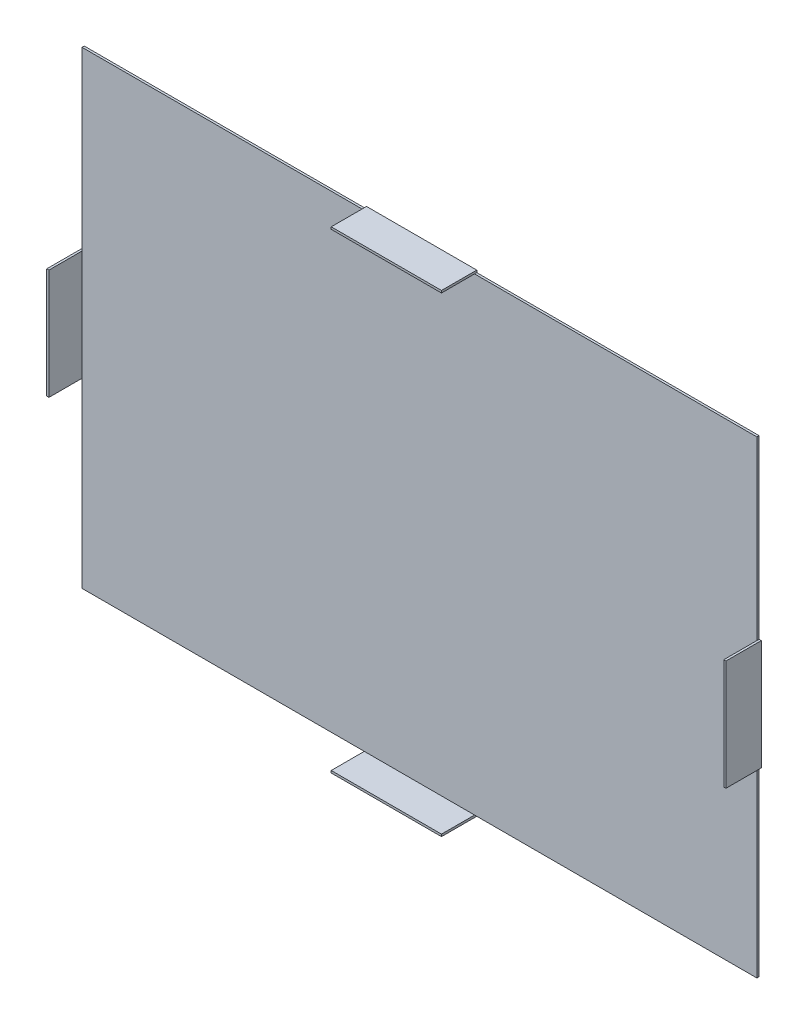
SolidWorks part; units mm, degrees
ref_plane "前基準面" through (0, 0, 0) normal (0, 0, 1) x (1, 0, 0)
ref_plane "上基準面" through (0, 0, 0) normal (0, 1, 0) x (1, 0, 0)
ref_plane "右基準面" through (0, 0, 0) normal (1, 0, 0) x (0, 0, -1)
sketch "草圖1" plane through (0, 0, 0) normal (0, 0, 1) x (1, 0, 0)
  line L1 (-301.7882, 224.6299) -> (310.2118, 224.6299)
  line L2 (-301.7882, 224.6299) -> (-301.7882, -200.3701)
  line L3 (-301.7882, -200.3701) -> (310.2118, -200.3701)
  line L4 (310.2118, 224.6299) -> (310.2118, -200.3701)
  dimension "D1" = 612
  dimension "D2" = 425
extrude "填料-伸長1" add sketch "草圖1" along normal blind 2
sketch "草圖2" plane through (0, -200.3701, 0) normal (0, -1, 0) x (1, 0, 0)
  line L0 (-301.7882, 0) -> (310.2118, 0) construction
  line L1 (-45.7882, 0) -> (54.2118, 0)
  line L2 (-45.7882, 0) -> (-45.7882, 32)
  line L3 (-45.7882, 32) -> (54.2118, 32)
  line L4 (54.2118, 0) -> (54.2118, 32)
  line L5 (-301.7882, 2) -> (-301.7882, 0) construction
  dimension "D1" = 32
  dimension "D2" = 100
  dimension "D3" = 256
extrude "填料-伸長2" add sketch "草圖2" along normal blind 2
sketch "草圖3" plane through (-301.7882, 0, 0) normal (-1, 0, 0) x (0, 0, 1)
  line L0 (0, 224.6299) -> (0, -200.3701) construction
  line L1 (0, 64.6299) -> (32, 64.6299)
  line L2 (0, 64.6299) -> (0, -35.3701)
  line L3 (0, -35.3701) -> (32, -35.3701)
  line L4 (32, 64.6299) -> (32, -35.3701)
  line L6 (2, 224.6299) -> (0, 224.6299) construction
  dimension "D1" = 32
  dimension "D2" = 100
  dimension "D3" = 160
extrude "填料-伸長3" add sketch "草圖3" along normal blind 2
sketch "草圖4" plane through (0, 224.6299, 0) normal (0, 1, 0) x (1, 0, 0)
  line L0 (310.2118, 0) -> (-301.7882, 0) construction
  line L1 (-45.7882, 0) -> (54.2118, 0)
  line L2 (-45.7882, 0) -> (-45.7882, -32)
  line L3 (-45.7882, -32) -> (54.2118, -32)
  line L4 (54.2118, 0) -> (54.2118, -32)
  line L5 (-301.7882, -2) -> (-301.7882, 0) construction
  dimension "D1" = 100
  dimension "D2" = 32
  dimension "D3" = 256
extrude "填料-伸長4" add sketch "草圖4" along normal blind 2
sketch "草圖5" plane through (310.2118, 0, 0) normal (1, 0, 0) x (0, 0, -1)
  line L1 (0, 64.6299) -> (-32, 64.6299)
  line L2 (0, 64.6299) -> (0, -35.3701)
  line L3 (0, -35.3701) -> (-32, -35.3701)
  line L4 (-32, 64.6299) -> (-32, -35.3701)
extrude "填料-伸長5" add sketch "草圖5" along normal blind 2
sketch "草圖6" plane through (0, 0, 0) normal (0, 0, -1) x (-1, 0, 0)
  line L1 (-265.4618, 25.1299) -> (-239.4618, 25.1299)
  line L2 (-265.4618, 25.1299) -> (-265.4618, -0.8701)
  line L3 (-265.4618, -0.8701) -> (-239.4618, -0.8701)
  line L4 (-239.4618, 25.1299) -> (-239.4618, -0.8701)
  line L5 (-310.2118, 224.6299) -> (-54.2118, 224.6299) construction
  line L6 (-310.2118, 64.6299) -> (-310.2118, 224.6299) construction
  line L7 (-4.2118, 226.6299) -> (-4.2118, -202.3701)
  line L8 (-267.4618, 27.1299) -> (-237.4618, 27.1299)
  line L9 (-267.4618, 27.1299) -> (-267.4618, -2.8701)
  line L10 (-267.4618, -2.8701) -> (-237.4618, -2.8701)
  line L11 (-237.4618, 27.1299) -> (-237.4618, -2.8701)
  line L12 (-54.2118, 226.6299) -> (45.7882, 226.6299) construction
  line L13 (45.7882, -202.3701) -> (-54.2118, -202.3701) construction
  line L14 (301.7882, -35.3701) -> (301.7882, -200.3701) construction
  line L15 (-310.2118, -200.3701) -> (-310.2118, -35.3701) construction
  line L16 (259.0382, -2.8701) -> (229.0382, -2.8701)
  line L17 (259.0382, 27.1299) -> (259.0382, -2.8701)
  line L18 (257.0382, -0.8701) -> (231.0382, -0.8701)
  line L19 (257.0382, 25.1299) -> (257.0382, -0.8701)
  line L20 (257.0382, 25.1299) -> (231.0382, 25.1299)
  line L21 (229.0382, 27.1299) -> (229.0382, -2.8701)
  line L22 (259.0382, 27.1299) -> (229.0382, 27.1299)
  line L23 (231.0382, 25.1299) -> (231.0382, -0.8701)
  dimension "D1" = 26
  dimension "D2" = 26
  dimension "D3" = 199.5
  dimension "D4" = 44.75
  dimension "D5" = 30
  dimension "D6" = 30
  dimension "D7" = 2
  dimension "D8" = 2
  dimension "D9" = 306
  dimension "D10" = 306
extrude "填料-伸長6" add sketch "草圖6" along normal blind 30 contours L17 L16 L21 L22 | L19 L18 L23 L20 | L10 L11 L8 L9 | L3 L4 L1 L2
sketch "草圖7" plane through (0, 0, 0) normal (0, 0, -1) x (-1, 0, 0)
  line L0 (-310.2118, 64.6299) -> (-310.2118, 224.6299) construction
  line L1 (-17.2118, 183.1299) -> (8.7882, 183.1299)
  line L2 (-17.2118, 183.1299) -> (-17.2118, 157.1299)
  line L3 (-17.2118, 157.1299) -> (8.7882, 157.1299)
  line L4 (8.7882, 183.1299) -> (8.7882, 157.1299)
  line L6 (8.7882, -132.8701) -> (-17.2118, -132.8701)
  line L7 (8.7882, -132.8701) -> (8.7882, -158.8701)
  line L8 (8.7882, -158.8701) -> (-17.2118, -158.8701)
  line L9 (-17.2118, -132.8701) -> (-17.2118, -158.8701)
  line L13 (10.7882, -130.8701) -> (-19.2118, -130.8701)
  line L14 (10.7882, -130.8701) -> (10.7882, -160.8701)
  line L15 (10.7882, -160.8701) -> (-19.2118, -160.8701)
  line L16 (-19.2118, -130.8701) -> (-19.2118, -160.8701)
  line L18 (45.7882, -200.3701) -> (-54.2118, -200.3701) construction
  line L19 (-310.2118, 224.6299) -> (-54.2118, 224.6299) construction
  line L21 (10.7882, 185.1299) -> (-19.2118, 185.1299)
  line L22 (10.7882, 185.1299) -> (10.7882, 155.1299)
  line L23 (10.7882, 155.1299) -> (-19.2118, 155.1299)
  line L24 (-19.2118, 185.1299) -> (-19.2118, 155.1299)
  point P22 (0, 0)
  point P23 (0, 0)
  point P24 (0, 0)
  point P25 (0, 0)
  point P26 (0, 0)
  point P27 (0, 0)
  point P28 (0, 0)
  point P29 (0, 0)
  point P30 (0, 0)
  point P31 (0, 0)
  dimension "D1" = 26
  dimension "D2" = 26
  dimension "D3" = 293
  dimension "D4" = 290
  dimension "D5" = 26
  dimension "D6" = 41.5
  dimension "D7" = 30
  dimension "D8" = 30
  dimension "D9" = 26
  dimension "D10" = 2
  dimension "D11" = 2
  dimension "D12" = 41.5
  dimension "D13" = 2
  dimension "D14" = 2
  dimension "D15" = 30
  dimension "D16" = 30
extrude "填料-伸長7" add sketch "草圖7" along normal blind 30 contours L21 L24 L23 L22 L1 L4 L3 L2 | L13 L16 L15 L14 | L6 L9 L8 L7
sketch "草圖8" plane through (0, 185.1299, 0) normal (0, 1, 0) x (1, 0, 0)
  line L0 (19.2118, 30) -> (19.2118, 0) construction
  line L1 (-10.7882, 30) -> (19.2118, 30) construction
  circle A0 centre (4.2118, 15) radius 2
  dimension "D3" = 4
  dimension "D1" = 15
  dimension "D2" = 15
extrude "除料-伸長1" cut sketch "草圖8" against normal through all
sketch "草圖9" plane through (-259.0382, 0, 0) normal (-1, 0, 0) x (0, 0, 1)
  line L0 (0, 27.1299) -> (0, -2.8701) construction
  line L1 (-30, -2.8701) -> (0, -2.8701) construction
  circle A0 centre (-15, 12.1299) radius 2
  dimension "D1" = 4
  dimension "D3" = 15
  dimension "D2" = 15
extrude "除料-伸長2" cut sketch "草圖9" against normal through all
